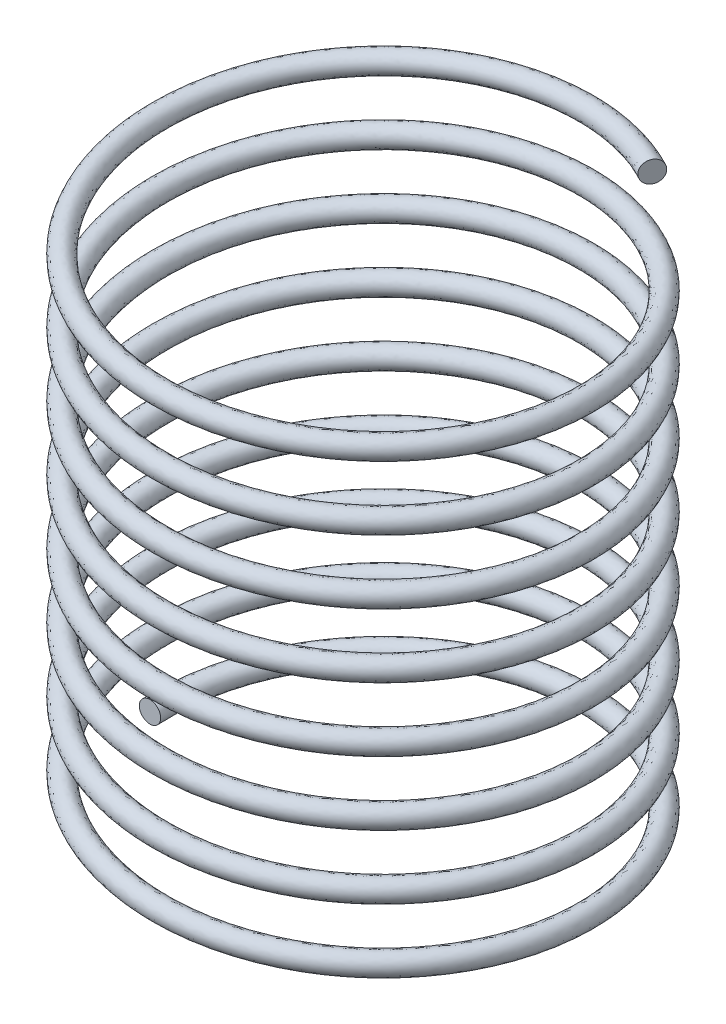
SolidWorks part; units mm, degrees
ref_plane "Front Plane" through (0, 0, 0) normal (0, 0, 1) x (1, 0, 0)
ref_plane "Top Plane" through (0, 0, 0) normal (0, 1, 0) x (1, 0, 0)
ref_plane "Right Plane" through (0, 0, 0) normal (1, 0, 0) x (0, 0, -1)
sketch "Sketch3" plane through (0, 0, 0) normal (0, 1, 0) x (1, 0, 0)
  circle A0 centre (0, 0) radius 10
  dimension "D1" = 20
curve "Helix/Spiral2" pitch 3 height 24.99 turns 8.33
sketch "Sketch4" plane through (0, 0, 0) normal (0, 0, 1) x (1, 0, 0)
  circle A0 centre (-10, 0) radius 0.5
  spline S0 degree 3 poles (-10, 0) (-10, 0.0622) (-9.4771, 0.1881) (-7.2439, 0.3757) (-3.9034, 0.5637) (0.0339, 0.7516) (3.966, 0.9395) (7.2918, 1.1274) (9.5029, 1.3153) (10.2612, 1.5032) (9.4509, 1.6911) (7.1957, 1.8789) (3.8405, 2.0668) (-0.1018, 2.2547) (-4.0285, 2.4426) (-7.3394, 2.6305) (-9.5283, 2.8184) (-10.2606, 3.0063) (-9.4242, 3.1942) (-7.1472, 3.3821) (-3.7775, 3.57) (0.1697, 3.7579) (4.0909, 3.9458) (7.3867, 4.1337) (9.5533, 4.3216) (10.2594, 4.5095) (9.3972, 4.6974) (7.0983, 4.8853) (3.7143, 5.0732) (-0.2375, 5.2611) (-4.153, 5.4489) (-7.4337, 5.6368) (-9.5779, 5.8247) (-10.2579, 6.0126) (-9.3697, 6.2005) (-7.0491, 6.3884) (-3.651, 6.5763) (0.3054, 6.7642) (4.215, 6.9521) (7.4803, 7.14) (9.602, 7.3279) (10.2558, 7.5158) (9.3418, 7.7037) (6.9997, 7.8916) (3.5875, 8.0795) (-0.3732, 8.2674) (-4.2768, 8.4553) (-7.5266, 8.6432) (-9.6257, 8.8311) (-10.2534, 9.0189) (-9.3135, 9.2068) (-6.9499, 9.3947) (-3.5238, 9.5826) (0.441, 9.7705) (4.3384, 9.9584) (7.5725, 10.1463) (9.649, 10.3342) (10.2505, 10.5221) (9.2848, 10.71) (6.8998, 10.8979) (3.46, 11.0858) (-0.5088, 11.2737) (-4.3998, 11.4616) (-7.6182, 11.6495) (-9.6719, 11.8374) (-10.2471, 12.0253) (-9.2557, 12.2132) (-6.8494, 12.4011) (-3.396, 12.5889) (0.5766, 12.7768) (4.461, 12.9647) (7.6635, 13.1526) (9.6944, 13.3405) (10.2433, 13.5284) (9.2262, 13.7163) (6.7987, 13.9042) (3.3319, 14.0921) (-0.6443, 14.28) (-4.522, 14.4679) (-7.7084, 14.6558) (-9.7164, 14.8437) (-10.239, 15.0316) (-9.1963, 15.2195) (-6.7478, 15.4074) (-3.2676, 15.5953) (0.712, 15.7832) (4.5829, 15.9711) (7.7531, 16.1589) (9.738, 16.3468) (10.2343, 16.5347) (9.166, 16.7226) (6.6965, 16.9105) (3.2032, 17.0984) (-0.7797, 17.2863) (-4.6435, 17.4742) (-7.7974, 17.6621) (-9.7592, 17.85) (-10.2292, 18.0379) (-9.1353, 18.2258) (-6.6449, 18.4137) (-3.1387, 18.6016) (0.8474, 18.7895) (4.7039, 18.9774) (7.8413, 19.1653) (9.78, 19.3532) (10.2235, 19.5411) (9.1042, 19.7289) (6.593, 19.9168) (3.074, 20.1047) (-0.915, 20.2926) (-4.7641, 20.4805) (-7.8849, 20.6684) (-9.8003, 20.8563) (-10.2175, 21.0442) (-9.0727, 21.2321) (-6.5409, 21.42) (-3.0092, 21.6079) (0.9826, 21.7958) (4.8241, 21.9837) (7.9282, 22.1716) (9.8202, 22.3595) (10.211, 22.5474) (9.0408, 22.7353) (6.4885, 22.9232) (2.9442, 23.1111) (-1.0501, 23.2989) (-4.8839, 23.4868) (-7.9711, 23.6747) (-9.8397, 23.8626) (-10.2041, 24.0505) (-9.0084, 24.2384) (-6.436, 24.4263) (-2.8782, 24.6143) (1.1142, 24.8019) (3.6754, 24.9278) (4.8175, 24.99) knots 0 0 0 0 0.007519 0.015038 0.022556 0.030075 0.037594 0.045113 0.052632 0.06015 0.067669 0.075188 0.082707 0.090226 0.097744 0.105263 0.112782 0.120301 0.12782 0.135338 0.142857 0.150376 0.157895 0.165414 0.172932 0.180451 0.18797 0.195489 0.203008 0.210526 0.218045 0.225564 0.233083 0.240602 0.24812 0.255639 0.263158 0.270677 0.278195 0.285714 0.293233 0.300752 0.308271 0.315789 0.323308 0.330827 0.338346 0.345865 0.353383 0.360902 0.368421 0.37594 0.383459 0.390977 0.398496 0.406015 0.413534 0.421053 0.428571 0.43609 0.443609 0.451128 0.458647 0.466165 0.473684 0.481203 0.488722 0.496241 0.503759 0.511278 0.518797 0.526316 0.533835 0.541353 0.548872 0.556391 0.56391 0.571429 0.578947 0.586466 0.593985 0.601504 0.609023 0.616541 0.62406 0.631579 0.639098 0.646617 0.654135 0.661654 0.669173 0.676692 0.684211 0.691729 0.699248 0.706767 0.714286 0.721805 0.729323 0.736842 0.744361 0.75188 0.759398 0.766917 0.774436 0.781955 0.789474 0.796992 0.804511 0.81203 0.819549 0.827068 0.834586 0.842105 0.849624 0.857143 0.864662 0.87218 0.879699 0.887218 0.894737 0.902256 0.909774 0.917293 0.924812 0.932331 0.93985 0.947368 0.954887 0.962406 0.969925 0.977444 0.984962 0.992481 1 1 1 1 construction
  dimension "D1" = 1
sweep "Sweep1" add profiles "Sketch4" path "Helix/Spiral2"
